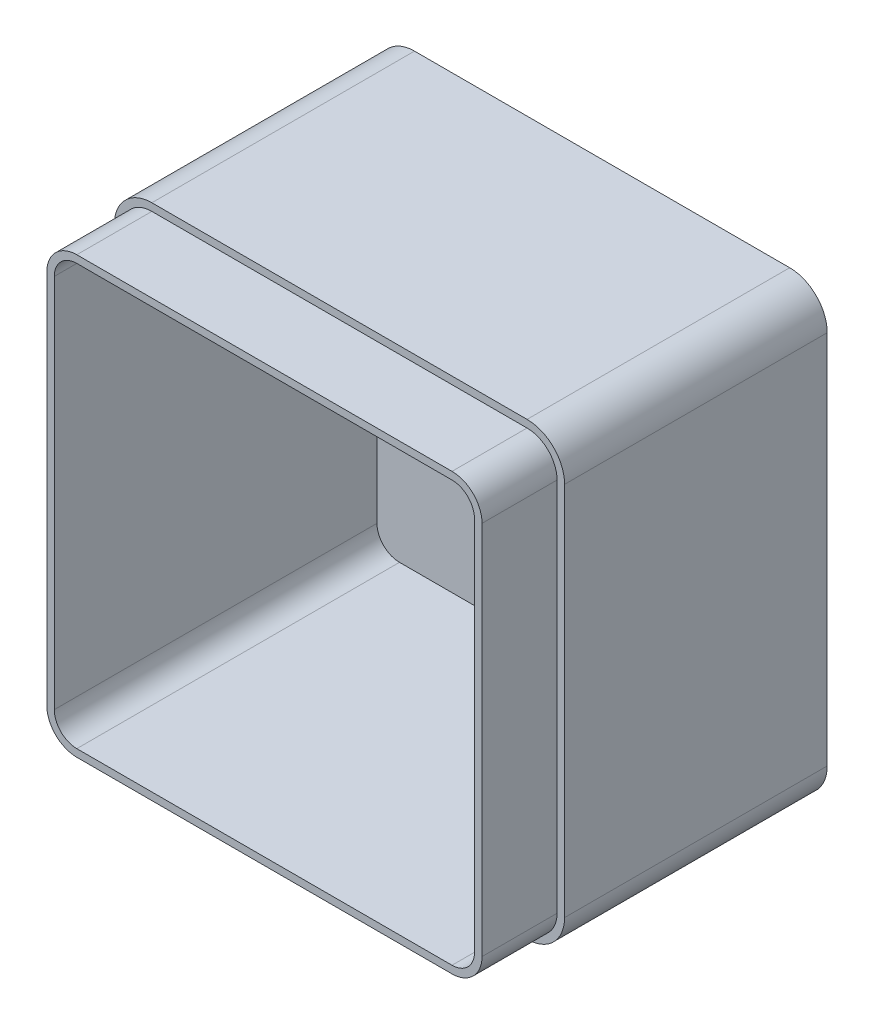
SolidWorks part; units mm, degrees
ref_plane "Front Plane" through (0, 0, 0) normal (0, 0, 1) x (1, 0, 0)
ref_plane "Top Plane" through (0, 0, 0) normal (0, 1, 0) x (1, 0, 0)
ref_plane "Right Plane" through (0, 0, 0) normal (1, 0, 0) x (0, 0, -1)
sketch "Sketch2" plane through (0, 0, 0) normal (0, 0, 1) x (1, 0, 0)
  line L1 (0, 0) -> (120, 0)
  line L2 (0, 0) -> (0, 120)
  line L3 (0, 120) -> (120, 120)
  line L4 (120, 0) -> (120, 120)
  dimension "D1" = 120
  dimension "D2" = 120
extrude "Boss-Extrude1" add sketch "Sketch2" along normal blind 90
fillet "Fillet1" radius 10 4 edges at (120, 0, 45) (0, 0, 45) (120, 120, 45) (0, 120, 45)
shell "Shell2" thickness 4
sketch "Sketch3" plane through (0, 0, 90) normal (0, 0, 1) x (1, 0, 0)
  line L0 (10, 2) -> (110, 2)
  line L1 (118, 10) -> (118, 110)
  line L2 (110, 118) -> (10, 118)
  line L3 (2, 110) -> (2, 10)
  line L4 (10, 0) -> (110, 0)
  line L5 (120, 10) -> (120, 110)
  line L6 (110, 120) -> (10, 120)
  line L7 (0, 110) -> (0, 10)
  line L8 (10, 0) -> (110, 0)
  line L9 (120, 10) -> (120, 110)
  line L10 (110, 120) -> (10, 120)
  line L11 (0, 110) -> (0, 10)
  arc A0 (110, 2) -> (118, 10) centre (110, 10) ccw
  arc A1 (118, 110) -> (110, 118) centre (110, 110) ccw
  arc A2 (10, 118) -> (2, 110) centre (10, 110) ccw
  arc A3 (2, 10) -> (10, 2) centre (10, 10) ccw
  arc A4 (110, 0) -> (120, 10) centre (110, 10) ccw
  arc A5 (120, 110) -> (110, 120) centre (110, 110) ccw
  arc A6 (10, 120) -> (0, 110) centre (10, 110) ccw
  arc A7 (0, 10) -> (10, 0) centre (10, 10) ccw
  arc A8 (110, 0) -> (120, 10) centre (110, 10) ccw
  arc A9 (120, 110) -> (110, 120) centre (110, 110) ccw
  arc A10 (10, 120) -> (0, 110) centre (10, 110) ccw
  arc A11 (0, 10) -> (10, 0) centre (10, 10) ccw
  point P24 (0, 0)
  dimension "D1" = 0
extrude "Cut-Extrude3" cut sketch "Sketch3" along normal blind 20 and the other way blind 20
